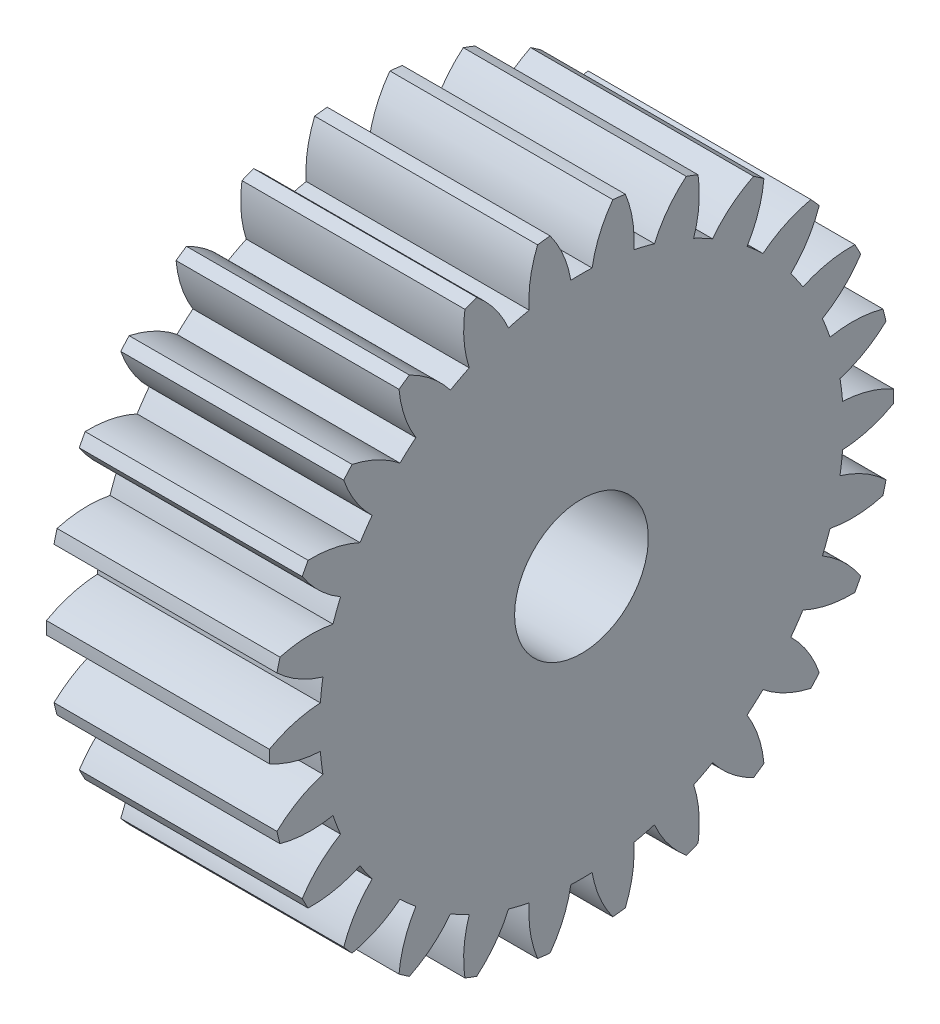
SolidWorks part; units mm, degrees
ref_plane "Plane1" through (0, 0, 0) normal (0, 0, 1) x (1, 0, 0)
ref_plane "Plane2" through (0, 0, 0) normal (0, 1, 0) x (1, 0, 0)
ref_plane "Plane3" through (0, 0, 0) normal (1, 0, 0) x (0, 0, -1)
other "Configuration Table"
sketch "HoldingSke" plane through (0, 0, 0) normal (0, 1, 0) x (1, 0, 0)
  line L0 (0, 0) -> (0.8988, -0.4384)
  line L1 (-15, 0) -> (100, 0) construction
  line L2 (0, 0) -> (-2.1039, 2.3779)
  line L3 (0, 0) -> (-11.863, 4.5341)
  line L4 (0, 0) -> (7.762, 3.7858)
  line L5 (0, 0) -> (-46.8476, -17.4728)
  line L6 (0, 0) -> (-8.2896, -5.593)
  line L7 (-2.1039, 2.3779) -> (8.6586, 51.2059)
  line L8 (-76.2, 54.61) -> (-75.2, 54.61)
  line L9 (-71.009, 38.7566) -> (-53.1078, 45.2721)
  line L10 (-76.2, 71.12) -> (104.1128, 71.12)
  line L11 (0, 0) -> (-10, 0)
  line L12 (-76.2, 101.6) -> (-76.162, 101.6)
  line L13 (24.9733, 27.94) -> (52.9518, 28.4284)
  line L14 (24.9733, 27.94) -> (24.9743, 27.94)
  line L15 (24.9733, 27.94) -> (100.4006, 29.5858)
  line L16 (-63.627, -1) -> (-12.827, -1)
  circle A0 centre (0, 0) radius 3
  circle A1 centre (0, 0) radius 11.749
  circle A2 centre (0, 0) radius 37.5
  circle A3 centre (0, 0) radius 3
  dimension "MHD" = 23.498
  dimension "Hub_dia" = 75
  dimension "Bore" = 6
  dimension "MBD" = 6
  dimension "Num_teeth" = 26
  dimension "Pitch" = 1
  dimension "Overall_len" = 50
  dimension "Show_teeth" = 26
  dimension "Thickness" = 10
  dimension "OAL" = 50.0001
  dimension "T_dim" = 1
  dimension "Ap" = 20
  dimension "H" = 19.05
  dimension "Pitch_radius" = 180.3128
  dimension "Width" = 10
  dimension "Backlash" = 0.038
  dimension "Addendum_fac" = 1
  dimension "Dedendum_fac" = 1.25
  dimension "Clearance_fac" = 0.25
  dimension "Dedendum_add" = 0.001
  dimension "Module" = 1
sketch "BasProSke" plane through (0, 0, 0) normal (0, 1, 0) x (1, 0, 0)
  line L0 (-10, 0) -> (60, 0) construction
  line L1 (0, 0) -> (0, 14)
  line L2 (0, 0) -> (10, 0)
  line L3 (10, 0) -> (10, 14)
  line L4 (10, 14) -> (0, 14)
  dimension "Thickness" = 10
  dimension "Diameter" = 28
revolve "Base-Revolve" add sketch "BasProSke" angle 360 about L0
sketch "TooCutSke" plane through (0, 0, 0) normal (1, 0, 0) x (0, 0, -1)
  line L1 (0, 0) -> (0, 107) construction
  line L2 (0, 0) -> (-0.8514, 12.9721) construction
  line L3 (0, 0) -> (-3.1292, 25.771) construction
  line L4 (-0.8514, 12.9721) -> (-1.5646, 12.8855) construction
  arc A0 (0.477, 11.7393) -> (-0.477, 11.7393) centre (0, 0) ccw
  arc A1 (1.4241, 13.9529) -> (-1.4241, 13.9529) centre (0, 0) ccw
  circle A2 centre (0, 0) radius 13 construction
  circle A3 centre (0, 0) radius 12.216 construction
  arc A4 (-0.477, 11.7393) -> (-1.4241, 13.9529) centre (-5.6014, 10.8561) ccw
  arc A5 (1.4241, 13.9529) -> (0.477, 11.7393) centre (5.6014, 10.8561) ccw
  dimension "Root_dia" = 23.498
  dimension "Overcut_dia" = 28.0508
  dimension "Pitch_dia" = 26
  dimension "Base_dia" = 24.432
  dimension "Flank_rad" = 5.2
  dimension "Half_ang" = 6.923
  dimension "Half_CT" = 0.7184
extrude "ToothCut" cut sketch "TooCutSke" along normal through all
fillet "Breaks" [suppressed] radius 0.02
fillet "RootFillets" [suppressed] radius 0.251
pattern_circular "TeethCuts" count 26 every 13.846 about axis through (-10, 0, 0) along (1, 0, 0) of "ToothCut", "RootFillets", "Breaks"
sketch "HubNeaOneSke" plane through (0, 0, 0) normal (-1, 0, 0) x (0, 0, 1)
  circle A0 centre (0, 0) radius 11.749
  dimension "Diameter" = 23.498
extrude "HubNearOne" [suppressed] add sketch "HubNeaOneSke" along normal blind 40.0001
sketch "HubNeaBotSke" plane through (0, 0, 0) normal (-1, 0, 0) x (0, 0, 1)
  circle A0 centre (0, 0) radius 11.749
  dimension "Diameter" = 23.498
extrude "HubNearBoth" [suppressed] add sketch "HubNeaBotSke" along normal blind 20
ref_plane "FarPln" through (10, 0, 0) normal (1, 0, 0) x (0, 0, -1)
sketch "HubFarSke" plane through (10, 0, 0) normal (1, 0, 0) x (0, 0, -1)
  circle A0 centre (0, 0) radius 11.749
  dimension "Diameter" = 23.498
extrude "HubFar" [suppressed] add sketch "HubFarSke" along normal blind 20
sketch "BorSke" plane through (0, 0, 0) normal (1, 0, 0) x (0, 0, -1)
  circle A0 centre (0, 0) radius 3
  dimension "Diameter" = 6
extrude "Bore" cut sketch "BorSke" along normal mid plane 100.0001
sketch "KeySke" plane through (0, 0, 0) normal (1, 0, 0) x (0, 0, -1)
  line L0 (-1, 0) -> (-1, 4)
  line L1 (-1, 4) -> (1, 4)
  line L2 (1, 4) -> (1, 0)
  line L3 (0, 0) -> (0, 34) construction
  line L4 (-1, 0) -> (1, 0)
  dimension "Offset" = 4
  dimension "Width" = 2
extrude "Keyway" [suppressed] cut sketch "KeySke" along normal mid plane 100.0001
pattern_circular "Keyway2" [suppressed] count 2 every 90 about axis through (-10, 0, 0) along (1, 0, 0)
equation "' \"Module@HoldingSke\" = 6.35"
equation "' \"Num_teeth@HoldingSke\" = 12"
equation "' \"Ap@HoldingSke\" =  20"
equation "' \"Ap@HoldingSke\" = 20"
equation "' \"Width@HoldingSke\" = 0.5 * 25.4"
equation "' \"Hub_dia@HoldingSke\"= 1 * 25.4"
equation "' \"Hub_dia@HoldingSke\" = 1 * 25.4"
equation "' \"Overall_len@HoldingSke\" = 1.0 * 25.4"
equation "' \"Bore@HoldingSke\" = 0.75 * 25.4"
equation "' \"T_dim@HoldingSke\" = 0.1 * 25.4"
equation "' \"Width@KeySke\" = 0.25 * 25.4"
equation "' \"Show_teeth@HoldingSke\" = 13"
equation "' \"Backlash@HoldingSke\" = 0.009 * 25.4"
equation "' \"Addendum_fac@HoldingSke\" = 1.0"
equation "' \"Dedendum_fac@HoldingSke\" = 1.25"
equation "' \"Dedendum_add@HoldingSke\" = 0.00005 * 25.4"
equation "' \"Clearance_fac@HoldingSke\" = 0.25"
equation "\"Pitch@HoldingSke\" = 1 / \"Module@HoldingSke\""
equation "\"Overcut_dia@TooCutSke\" = (\"Num_teeth@HoldingSke\" + 2 * \"Addendum_fac@HoldingSke\") / \"Pitch@HoldingSke\" + 0.002 * 25.4"
equation "\"Pitch_dia@TooCutSke\" = \"Num_teeth@HoldingSke\" / \"Pitch@HoldingSke\""
equation "\"Base_dia@TooCutSke\" = \"Num_teeth@HoldingSke\" / \"Pitch@HoldingSke\" * cos((\"Ap@HoldingSke\"  * 3.14159265 / 180))"
equation "\"Root_dia@TooCutSke\" = (\"Num_teeth@HoldingSke\" + 2) / \"Pitch@HoldingSke\" - 2 * (\"Addendum_fac@HoldingSke\" + \"Dedendum_fac@HoldingSke\") / \"Pitch@HoldingSke\" - \"Dedendum_add@HoldingSke\" * 2"
equation "\"Half_ang@TooCutSke\" = 180 / \"Num_teeth@HoldingSke\""
equation "\"Half_CT@TooCutSke\" = \"Num_teeth@HoldingSke\" / \"Pitch@HoldingSke\" * sin((3.14159265 / 2 / \"Num_teeth@HoldingSke\")) / 2 - 7 * \"Backlash@HoldingSke\" / 4"
equation "\"Flank_rad@TooCutSke\" = \"Num_teeth@HoldingSke\" / \"Pitch@HoldingSke\" / 5"
equation "\"Radius@RootFillets\" = \"Clearance_fac@HoldingSke\" / \"Pitch@HoldingSke\" + \"Dedendum_add@HoldingSke\""
equation "\"Break_rad@Breaks\" = 0.02 / \"Pitch@HoldingSke\""
equation "\"Thickness@HoldingSke\" = \"Width@HoldingSke\""
equation "\"OAL@HoldingSke\" = \"Thickness@HoldingSke\""
equation "\"MHD@HoldingSke\" = (\"Num_teeth@HoldingSke\" + 2) / \"Pitch@HoldingSke\" - 2 * (\"Addendum_fac@HoldingSke\" + \"Dedendum_fac@HoldingSke\")  / \"Pitch@HoldingSke\" - \"Dedendum_add@HoldingSke\" * 2"
equation "\"MBD@HoldingSke\" = (\"Num_teeth@HoldingSke\" + 2) / \"Pitch@HoldingSke\" - 2 * (\"Addendum_fac@HoldingSke\" + \"Dedendum_fac@HoldingSke\")  / \"Pitch@HoldingSke\" - \"Dedendum_add@HoldingSke\" * 2 - 0.002 * 25.4"
equation "\"MHD@HoldingSke\" = ((sgn( \"MHD@HoldingSke\" - \"Hub_dia@HoldingSke\" )-1)*( \"MHD@HoldingSke\" - \"Hub_dia@HoldingSke\" ))/-2+ \"Hub_dia@HoldingSke\""
equation "\"MBD@HoldingSke\" = ((sgn( \"MBD@HoldingSke\" - \"Bore@HoldingSke\" )-1)*( \"MBD@HoldingSke\" - \"Bore@HoldingSke\" ))/-2+ \"Bore@HoldingSke\""
equation "\"OAL@HoldingSke\" = ((sgn( \"OAL@HoldingSke\" - \"Overall_len@HoldingSke\" )+1)*( \"OAL@HoldingSke\" - \"Overall_len@HoldingSke\" ))/2 + \"Overall_len@HoldingSke\" + 0.000002 * 25.4"
equation "\"Num_teeth@TeethCuts\" = int( \"Show_teeth@HoldingSke\" ) + 1"
equation "\"Num_teeth@TeethCuts\" = ((sgn( \"Num_teeth@TeethCuts\" - \"Num_teeth@HoldingSke\" )-1)*( \"Num_teeth@TeethCuts\" - \"Num_teeth@HoldingSke\" ))/-2+ \"Num_teeth@HoldingSke\""
equation "\"Num_teeth@TeethCuts\" = ((sgn( \"Num_teeth@TeethCuts\" - 2.0)+1)*( \"Num_teeth@TeethCuts\" - 2.0))/2 +2.0"
equation "\"Angle@TeethCuts\" = 360.0 / \"Num_teeth@HoldingSke\""
equation "\"Diameter@BasProSke\" = (\"Num_teeth@HoldingSke\" + 2 * \"Addendum_fac@HoldingSke\") / \"Pitch@HoldingSke\""
equation "\"Thickness@BasProSke\"  = \"Thickness@HoldingSke\""
equation "' \"Fillet_rad@BasProSke\" =  \"Thickness@HoldingSke\" * 0.05"
equation "' \"Fillet_rad@BasProSke\" = \"Thickness@HoldingSke\" * 0.05"
equation "\"MHD@HoldingSke\" = ((sgn( \"MHD@HoldingSke\" - \"Root_dia@TooCutSke\" )-1)*( \"MHD@HoldingSke\" - \"Root_dia@TooCutSke\" ))/-2+ \"Root_dia@TooCutSke\""
equation "\"Diameter@HubNeaOneSke\" = \"MHD@HoldingSke\""
equation "\"Length@HubNearOne\" = \"OAL@HoldingSke\" - \"Thickness@BasProSke\""
equation "\"Diameter@HubNeaBotSke\" = \"MHD@HoldingSke\""
equation "\"Length@HubNearBoth\" = ( \"OAL@HoldingSke\" - \"Thickness@BasProSke\" ) / 2.0"
equation "\"Thickness@FarPln\" = \"Thickness@BasProSke\""
equation "\"Diameter@HubFarSke\" = \"MHD@HoldingSke\""
equation "\"Length@HubFar\" = ( \"OAL@HoldingSke\" - \"Thickness@BasProSke\" ) / 2.0"
equation "\"Diameter@BorSke\" = \"MBD@HoldingSke\""
equation "\"D1@Bore\" = \"OAL@HoldingSke\" * 2.0"
equation "\"D1@Keyway\" = \"OAL@HoldingSke\" * 2.0"
equation "\"Offset@KeySke\" = \"T_dim@HoldingSke\" + \"MBD@HoldingSke\" / 2.0"
